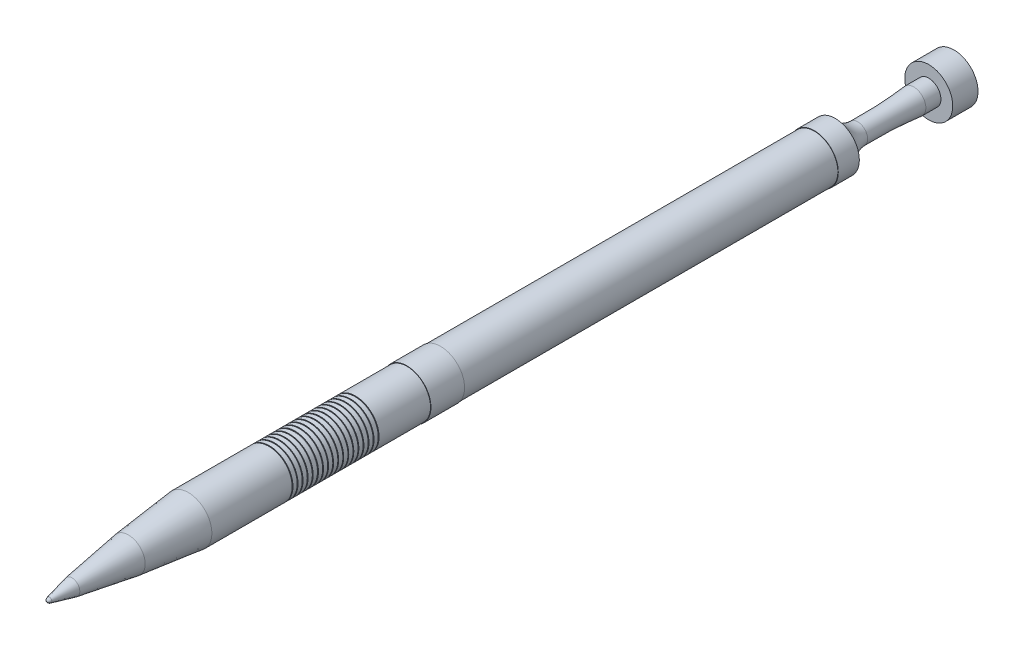
SolidWorks part; units mm, degrees
ref_plane "Front Plane" through (0, 0, 0) normal (0, 0, 1) x (1, 0, 0)
ref_plane "Top Plane" through (0, 0, 0) normal (0, 1, 0) x (1, 0, 0)
ref_plane "Right Plane" through (0, 0, 0) normal (1, 0, 0) x (0, 0, -1)
sketch "Sketch1" plane through (0, 0, 0) normal (1, 0, 0) x (0, 0, -1)
  line L0 (84.964, -57.8906) -> (566.2974, -57.8906) construction
  line L1 (4.7477, 4.3653) -> (39.6228, 13.8742)
  line L2 (39.6228, 13.8742) -> (138.7238, 26.3428)
  line L3 (138.7238, 26.3428) -> (244.7503, 36.7057)
  line L4 (244.7503, 36.7057) -> (386.6495, 36.7057)
  line L5 (386.6495, 36.7057) -> (391.8236, 36.7057)
  line L6 (391.8236, 36.7057) -> (391.8236, 38.7467)
  line L7 (391.8236, 38.7467) -> (403.6324, 38.7467)
  line L8 (403.6324, 38.7467) -> (403.6324, 36.7057)
  line L9 (403.6324, 36.7057) -> (405.2069, 36.7057)
  line L10 (405.2069, 36.7057) -> (405.2069, 38.7467)
  line L11 (405.2069, 38.7467) -> (415.4411, 38.7467)
  line L12 (415.4411, 38.7467) -> (415.4411, 36.7057)
  line L13 (415.4411, 36.7057) -> (417.4879, 36.7057)
  line L14 (417.4879, 36.7057) -> (417.4879, 38.7467)
  line L15 (417.4879, 38.7467) -> (425.392, 38.7467)
  line L16 (425.392, 38.7467) -> (526.9066, 38.7467)
  line L17 (0, 0) -> (526.9066, 0) construction
  line L18 (526.9066, 38.7467) -> (526.9066, 0) construction
  line L19 (39.6228, 13.8742) -> (39.6228, 0) construction
  line L20 (138.7238, 26.3428) -> (138.7238, 0) construction
  line L21 (28.6331, 10.0261) -> (100.2478, 19.0364)
  line L22 (300.2156, 28) -> (300.2156, 26.5251)
  line L23 (0, 0) -> (380.7654, 0) construction
  line L24 (3.4309, 3.1545) -> (28.6331, 10.0261)
  line L25 (380.7654, 28) -> (380.7654, 0) construction
  line L26 (307.4066, 28) -> (380.7654, 28)
  line L27 (292.8199, 26.5251) -> (292.8199, 28)
  line L28 (301.6947, 26.5251) -> (301.6947, 28)
  line L29 (176.8671, 26.5251) -> (279.4095, 26.5251)
  line L30 (292.8199, 28) -> (300.2156, 28)
  line L31 (100.2478, 19.0364) -> (100.2478, 0) construction
  line L32 (283.1486, 28) -> (291.6821, 28)
  line L33 (291.6821, 26.5251) -> (292.8199, 26.5251)
  line L34 (279.4095, 26.5251) -> (283.1486, 26.5251)
  line L35 (301.6947, 28) -> (307.4066, 28)
  line L36 (100.2478, 19.0364) -> (176.8671, 26.5251)
  line L37 (28.6331, 10.0261) -> (28.6331, 0) construction
  line L38 (283.1486, 26.5251) -> (283.1486, 28)
  line L39 (300.2156, 26.5251) -> (301.6947, 26.5251)
  line L40 (291.6821, 28) -> (291.6821, 26.5251)
  spline S0 degree 2 poles (0, 0) (0.5875, 2.8198) (4.7477, 4.3653) knots 0 0 0 1 1 1
  spline S1 degree 2 poles (0, 0) (0.4245, 2.0377) (3.4309, 3.1545) knots 0 0 0 1 1 1
sketch "Sketch2" plane through (0, 0, 0) normal (1, 0, 0) x (0, 0, -1)
  line L0 (30, 9.3213) -> (97, 20)
  line L1 (263.5678, 28) -> (263.5678, 27)
  line L2 (0, 0) -> (354, 0) construction
  line L3 (3.1897, 2.9328) -> (30, 9.3213)
  line L4 (263.5678, 27) -> (264.5678, 27)
  line L5 (264.5678, 27) -> (264.5678, 28)
  line L6 (264.5678, 28) -> (269.5678, 28)
  line L7 (269.5678, 28) -> (269.5678, 27)
  line L8 (168.2334, 28) -> (263.5678, 28)
  line L9 (269.5678, 27) -> (270.5678, 27)
  line L10 (97, 20) -> (97, 0) construction
  line L11 (270.5678, 27) -> (270.5678, 28)
  line L12 (270.5678, 28) -> (275.5678, 28)
  line L13 (275.5678, 28) -> (275.5678, 27)
  line L14 (275.5678, 27) -> (276.5678, 27)
  line L15 (97, 20) -> (168.2334, 28)
  line L16 (30, 9.3213) -> (30, 0) construction
  line L17 (276.5678, 27) -> (276.5678, 28)
  line L18 (276.5678, 28) -> (281.5678, 28)
  line L19 (281.5678, 28) -> (281.5678, 27)
  line L20 (281.5678, 27) -> (282.5678, 27)
  line L21 (428, 28) -> (428, 28.5)
  line L22 (428, 28.5) -> (468, 28.5)
  line L23 (468, 28.5) -> (468, 28)
  line L24 (282.5678, 27) -> (282.5678, 28)
  line L25 (282.5678, 28) -> (287.5678, 28)
  line L26 (287.5678, 28) -> (287.5678, 27)
  line L27 (287.5678, 27) -> (288.5678, 27)
  line L28 (288.5678, 27) -> (288.5678, 28)
  line L29 (288.5678, 28) -> (293.5678, 28)
  line L30 (293.5678, 28) -> (293.5678, 27)
  line L31 (293.5678, 27) -> (294.8799, 27)
  line L32 (294.8799, 27) -> (294.8799, 28)
  line L33 (294.8799, 28) -> (299.8799, 28)
  line L34 (299.8799, 28) -> (299.8799, 27)
  line L35 (299.8799, 27) -> (300.8799, 27)
  line L36 (300.8799, 27) -> (300.8799, 28)
  line L37 (300.8799, 28) -> (305.8799, 28)
  line L38 (305.8799, 28) -> (305.8799, 27)
  line L39 (305.8799, 27) -> (306.8799, 27)
  line L40 (306.8799, 27) -> (306.8799, 28)
  line L41 (306.8799, 28) -> (311.8799, 28)
  line L42 (311.8799, 28) -> (311.8799, 27)
  line L44 (311.8799, 27) -> (312.8799, 27)
  line L45 (312.8799, 27) -> (312.8799, 28)
  line L46 (312.8799, 28) -> (317.8799, 28)
  line L47 (317.8799, 28) -> (317.8799, 27)
  line L48 (317.8799, 27) -> (318.8799, 27)
  line L49 (318.8799, 27) -> (318.8799, 28)
  line L51 (318.8799, 28) -> (323.8799, 28)
  line L52 (323.8799, 28) -> (323.8799, 27)
  line L53 (323.8799, 27) -> (324.8799, 27)
  line L54 (324.8799, 27) -> (324.8799, 28)
  line L55 (324.8799, 28) -> (329.8799, 28)
  line L56 (329.8799, 28) -> (329.8799, 27)
  line L57 (329.8799, 27) -> (330.8799, 27)
  line L58 (330.8799, 27) -> (330.8799, 28)
  line L59 (330.8799, 28) -> (335.8799, 28)
  line L60 (335.8799, 28) -> (335.8799, 27)
  line L61 (335.8799, 27) -> (336.8799, 27)
  line L62 (336.8799, 27) -> (336.8799, 28)
  line L63 (336.8799, 28) -> (341.8799, 28)
  line L64 (341.8799, 28) -> (341.8799, 27)
  line L65 (341.8799, 27) -> (342.8799, 27)
  line L66 (342.8799, 27) -> (342.8799, 28)
  line L67 (342.8799, 28) -> (347.8799, 28)
  line L68 (347.8799, 28) -> (347.8799, 27)
  line L69 (347.8799, 27) -> (348.8799, 27)
  line L70 (348.8799, 27) -> (348.8799, 28)
  line L71 (348.8799, 28) -> (353.8799, 28)
  line L72 (353.8799, 28) -> (353.8799, 27)
  line L73 (353.8799, 27) -> (354.8799, 27)
  line L74 (354.8799, 27) -> (354.8799, 28)
  line L75 (354.8799, 28) -> (359.8799, 28)
  line L76 (359.8799, 28) -> (359.8799, 27)
  line L77 (359.8799, 27) -> (360.8799, 27)
  line L78 (360.8799, 27) -> (360.8799, 28)
  line L79 (360.8799, 28) -> (365.8799, 28)
  line L80 (365.8799, 28) -> (365.8799, 27)
  line L81 (365.8799, 27) -> (366.8799, 27)
  line L82 (366.8799, 27) -> (366.8799, 28)
  line L83 (366.8799, 28) -> (372.5678, 28)
  line L84 (0, 0) -> (1078, 0)
  line L88 (372.5678, 28) -> (428, 28)
  line L89 (354, 0) -> (1078, 0) construction
  line L90 (468, 28) -> (912, 28)
  line L91 (912, 28) -> (912, 28.5)
  line L92 (912, 28.5) -> (937, 28.5)
  line L93 (1048, 14.4588) -> (1048, 28.5)
  line L94 (1030.0861, 14.4588) -> (1048, 14.4588)
  line L95 (1048, 28.5) -> (1078, 28.5)
  line L96 (0, 0) -> (1078, 0) construction
  line L97 (1078, 28.5) -> (1078, 0)
  line L98 (0, 0) -> (1200, 0) construction
  arc A0 (937, 28.5) -> (963.5539, 11.8141) centre (964.1594, 42.2496) ccw
  arc A1 (963.5539, 11.8141) -> (1030.0861, 14.4588) centre (974.6673, 570.4241) ccw
  arc A2 (0, 0) -> (3.1897, 2.9328) centre (3.6405, -0.7585) cw
  dimension "D1" = 354
  dimension "D2" = 20
  dimension "D4" = 324
  dimension "D5" = 257
  dimension "D7" = 28
  dimension "D12" = 25
  dimension "D13" = 40
  dimension "D25" = 28.5
  dimension "D26" = 444
  dimension "D27" = 30
  dimension "D28" = 1078
  dimension "D29" = 28.5
sketch "Sketch3" plane through (0, 0, 0) normal (1, 0, 0) x (0, 0, -1)
  line L0 (-187.3872, -366.4554) -> (1001.9461, -366.4554) construction
  line L1 (0, 0) -> (909.9428, 0) construction
  line L2 (671.6231, 82.9347) -> (762.8319, 82.9347)
  line L3 (762.8319, 82.9347) -> (762.8319, 163.4739)
  line L4 (762.8319, 163.4739) -> (861.6904, 163.4739)
  line L5 (861.6904, 163.4739) -> (861.6904, 0)
  line L6 (132.9919, 14.4588) -> (132.9919, 28.5)
  line L7 (117.0906, 14.4588) -> (132.9919, 14.4588)
  line L8 (132.9919, 28.5) -> (150.2269, 28.5)
  line L9 (0, 0) -> (158.6392, 0) construction
  line L10 (150.2269, 28.5) -> (150.2269, 0)
  spline S0 degree 3 poles (137.6877, 163.4739) (148.0153, 143.0739) (169.0219, 114.389) (207.4301, 86.7303) (246.2049, 75.27) (300.3386, 63.9116) (357.0718, 67.3275) (412.8153, 66.2896) (456.9068, 66.3299) (502.306, 70.4068) (573.9179, 72.2312) (630.0541, 77.1645) (671.6231, 82.9347) knots 0 0 0 0 0.120101 0.183568 0.24453 0.330744 0.473082 0.540421 0.623868 0.704384 0.779647 1 1 1 1
  spline S1 degree 3 poles (24.0044, 28.5) (25.805, 24.9435) (29.4672, 19.9425) (36.1633, 15.1205) (42.9233, 13.1225) (52.3609, 11.1423) (62.2518, 11.7379) (71.9701, 11.5569) (79.657, 11.5639) (87.5719, 12.2747) (100.0567, 12.5928) (109.8434, 13.4528) (117.0906, 14.4588) knots 0 0 0 0 0.120101 0.183568 0.24453 0.330744 0.473082 0.540421 0.623868 0.704384 0.779647 1 1 1 1
  dimension "D1" = 163.4739
  dimension "D2" = 163.4739
revolve "Revolve3" add sketch "Sketch2" angle 360 about L98
